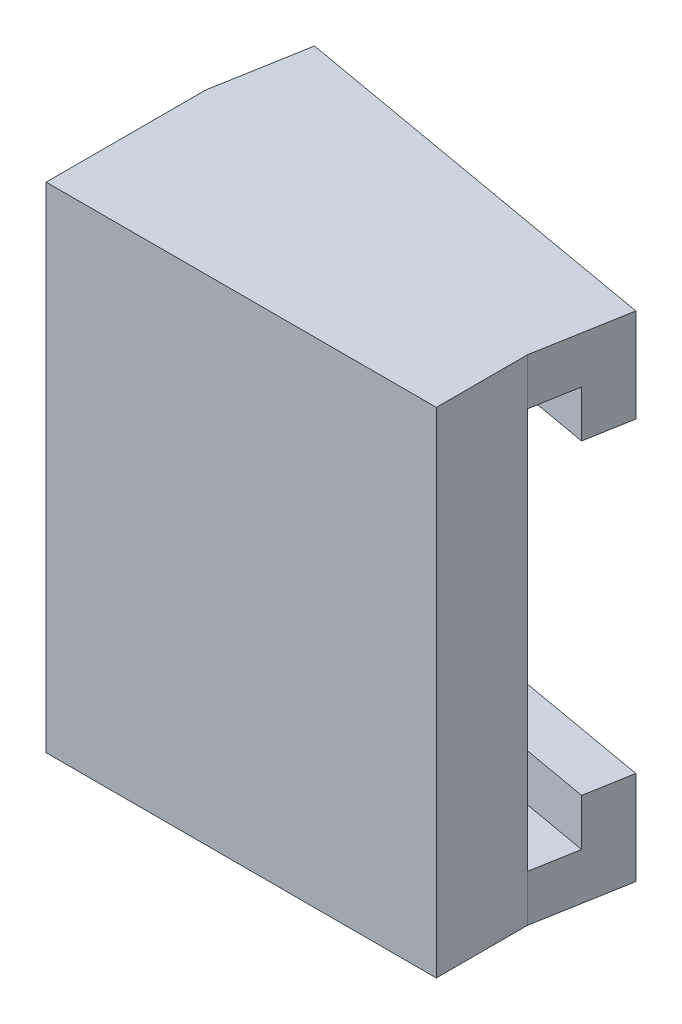
SolidWorks part; units mm, degrees
ref_plane "Ebene vorne" through (0, 0, 0) normal (0, 0, 1) x (1, 0, 0)
ref_plane "Ebene oben" through (0, 0, 0) normal (0, 1, 0) x (1, 0, 0)
ref_plane "Ebene rechts" through (0, 0, 0) normal (1, 0, 0) x (0, 0, -1)
sketch "Skizze1" plane through (0, 0, 0) normal (0, 0, 1) x (1, 0, 0)
  line L1 (-7.5, -9.5) -> (7.5, -9.5)
  line L2 (-7.5, -9.5) -> (-7.5, 9.5)
  line L3 (-7.5, 9.5) -> (7.5, 9.5)
  line L4 (7.5, -9.5) -> (7.5, 9.5)
  line L5 (-7.5, -9.5) -> (7.5, 9.5) construction
  line L6 (-7.5, 9.5) -> (7.5, -9.5) construction
  point P0 (0, 0)
  dimension "D1" = 15
  dimension "D2" = 19
extrude "Aufsatz-Linear austragen1" add sketch "Skizze1" along normal blind 3
sketch "Skizze3" plane through (0, 9.5, 0) normal (0, 1, 0) x (1, 0, 0)
  line L0 (-7.5, 0) -> (-7.5, 2.6449)
  line L1 (-7.5, 2.6449) -> (7.5, 0)
  line L2 (7.5, 0) -> (-7.5, 0) construction
  line L3 (-7.5, 0) -> (7.5, 0)
  dimension "D1" = 10
extrude "Aufsatz-Linear austragen2" add sketch "Skizze3" against normal blind 19
sketch "Skizze5" plane through (0, 0, 3) normal (0, 0, 1) x (1, 0, 0)
  circle A0 centre (0, 0) radius 3
  dimension "D1" = 6
extrude "Schnitt-Linear austragen1" cut sketch "Skizze5" against normal blind 3
sketch "Skizze6" plane through (0, 0, 3) normal (0, 0, 1) x (1, 0, 0)
  line L4 (7.5, -9.5) -> (7.5, 9.5)
  line L5 (7.5, 9.5) -> (-7.5, 9.5)
  line L6 (-7.5, 9.5) -> (-7.5, -9.5)
  line L7 (-7.5, -9.5) -> (7.5, -9.5)
  line L8 (7.5, -9.5) -> (7.5, 9.5)
  line L9 (7.5, 9.5) -> (-7.5, 9.5)
  line L10 (-7.5, 9.5) -> (-7.5, -9.5)
  line L11 (-7.5, -9.5) -> (7.5, -9.5)
  dimension "D1" = 0
extrude "Aufsatz-Linear austragen3" add sketch "Skizze6" along normal blind 0.5
sketch "Skizze7" plane through (0.2262, 0, -1.2826) normal (0.1736, 0, -0.9848) x (-0.9848, 0, -0.1736)
  line L0 (-7.3861, -9.5) -> (-7.3861, 9.5) construction
  line L1 (7.8453, 9.5) -> (-7.3861, 9.5)
  line L2 (7.8453, 9.5) -> (7.8453, 7.7)
  line L3 (7.8453, 7.7) -> (-7.3861, 7.7)
  line L4 (-7.3861, 9.5) -> (-7.3861, 7.7)
  line L5 (7.8453, -9.5) -> (7.8453, 9.5) construction
  line L6 (-7.3861, -9.5) -> (7.8453, -9.5)
  line L7 (-7.3861, -9.5) -> (-7.3861, -7.7)
  line L8 (-7.3861, -7.7) -> (7.8453, -7.7)
  line L9 (7.8453, -9.5) -> (7.8453, -7.7)
  dimension "D1" = 1.8
  dimension "D2" = 1.8
extrude "Aufsatz-Linear austragen4" add sketch "Skizze7" along normal blind 3.6
sketch "Skizze9" plane through (0, -7.7, 0) normal (0, 1, 0) x (1, 0, 0)
  line L0 (7.8126, 1.7727) -> (-7.1874, 4.4176)
  line L1 (8.1251, 3.5453) -> (7.5, 0) construction
  line L2 (-6.8749, 6.1902) -> (-7.5, 2.6449) construction
  line L3 (-7.1874, 4.4176) -> (-6.8749, 6.1902)
  line L4 (-6.8749, 6.1902) -> (8.1251, 3.5453)
  line L5 (8.1251, 3.5453) -> (7.8126, 1.7727)
  dimension "D1" = 1.8
sketch "Skizze10" plane through (0, 7.7, 0) normal (0, -1, 0) x (1, 0, 0)
  line L0 (8.1251, -3.5453) -> (7.8126, -1.7727)
  line L1 (8.1251, -3.5453) -> (7.5, 0) construction
  line L2 (7.8126, -1.7727) -> (-7.1874, -4.4176)
  line L3 (-6.8749, -6.1902) -> (-7.5, -2.6449) construction
  line L4 (-7.1874, -4.4176) -> (-6.8749, -6.1902)
  line L5 (-6.8749, -6.1902) -> (8.1251, -3.5453)
extrude "Aufsatz-Linear austragen5" add sketch "Skizze10" along normal blind 1.8
extrude "Aufsatz-Linear austragen6" add sketch "Skizze9" along normal blind 1.8
